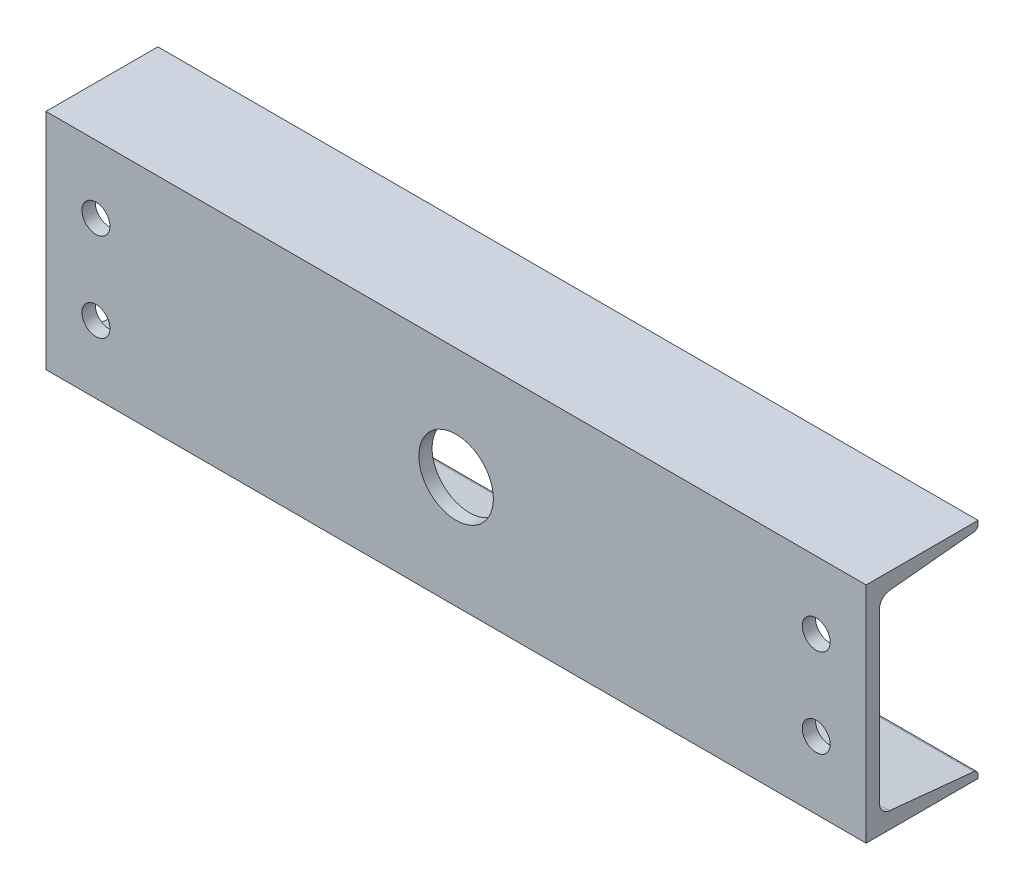
SolidWorks part; units mm, degrees
ref_plane "Front Plane" through (0, 0, 0) normal (0, 0, 1) x (1, 0, 0)
ref_plane "Top Plane" through (0, 0, 0) normal (0, 1, 0) x (1, 0, 0)
ref_plane "Right Plane" through (0, 0, 0) normal (1, 0, 0) x (0, 0, -1)
sketch "Sketch1" plane through (0, 0, 0) normal (1, 0, 0) x (0, 0, -1)
  line L0 (-48.8061, -76.2) -> (-48.8061, 76.2)
  line L1 (-48.8061, 76.2) -> (27.3939, 76.2)
  line L2 (-48.8061, -76.2) -> (27.3939, -76.2)
  line L3 (4.3561, -67.4878) -> (-21.0439, -67.4878) construction
  line L4 (-39.7637, 57.3918) -> (-39.7637, -57.3918)
  line L5 (27.3939, 76.2) -> (27.3939, 73.7107)
  line L6 (27.3939, -76.2) -> (27.3939, -73.7107)
  line L7 (-32.8952, 64.9747) -> (24.6465, 70.6776)
  line L8 (-32.8952, -64.9747) -> (24.6465, -70.6776)
  arc A0 (-39.7637, -57.3918) -> (-32.8952, -64.9747) centre (-32.1437, -57.3918) ccw
  arc A1 (-39.7637, 57.3918) -> (-32.8952, 64.9747) centre (-32.1437, 57.3918) cw
  arc A2 (27.3939, 73.7107) -> (24.6465, 70.6776) centre (24.3459, 73.7107) cw
  arc A3 (27.3939, -73.7107) -> (24.6465, -70.6776) centre (24.3459, -73.7107) ccw
  dimension "D1" = 76.2
  dimension "D2" = 9.0424
extrude "Boss-Extrude1" add sketch "Sketch1" along normal mid plane 558.8
sketch "Sketch2" plane through (0, 0, 48.8061) normal (0, 0, 1) x (1, 0, 0)
  circle A1 centre (0, 0) radius 25.4
  dimension "D1" = 50.8
extrude "Cut-Extrude1" cut sketch "Sketch2" against normal up to next
sketch "Sketch3" plane through (0, 0, 48.8061) normal (0, 0, 1) x (1, 0, 0)
  line L0 (279.4, 76.2) -> (-279.4, 76.2) construction
  line L1 (-279.4, 76.2) -> (-279.4, -76.2) construction
  line L2 (0, 76.2) -> (0, -76.2) construction
  line L3 (279.4, -76.2) -> (-279.4, -76.2) construction
  line L4 (-279.4, 0) -> (279.4, 0) construction
  line L5 (279.4, 76.2) -> (279.4, -76.2) construction
  circle A0 centre (-245.364, 30.1625) radius 9.525
  circle A1 centre (245.364, 30.1625) radius 9.525
  circle A2 centre (245.364, -30.1625) radius 9.525
  circle A3 centre (-245.364, -30.1625) radius 9.525
  dimension "D3" = 19.05
  dimension "D1" = 46.0375
  dimension "D2" = 34.036
extrude "Cut-Extrude2" cut sketch "Sketch3" against normal up to next
